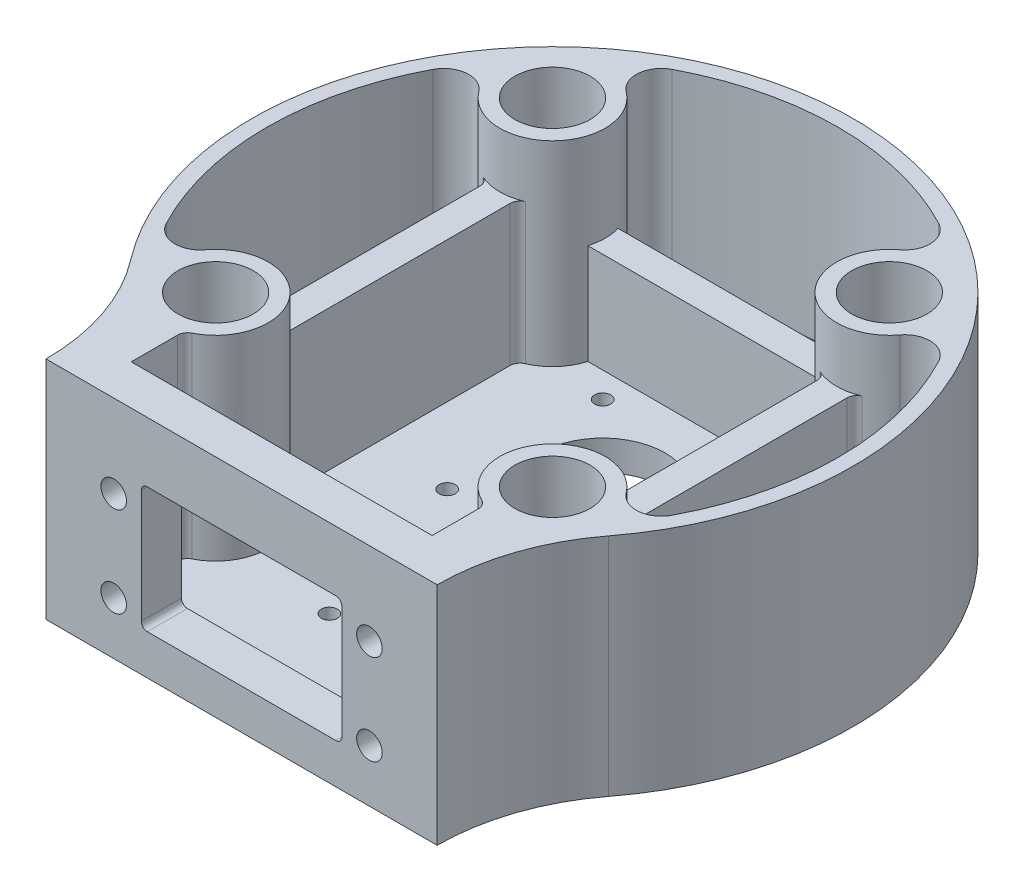
SolidWorks part; units mm, degrees
ref_plane "Front Plane" through (0, 0, 0) normal (0, 0, 1) x (1, 0, 0)
ref_plane "Top Plane" through (0, 0, 0) normal (0, 1, 0) x (1, 0, 0)
ref_plane "Right Plane" through (0, 0, 0) normal (1, 0, 0) x (0, 0, -1)
sketch "Sketch1" plane through (0, 0, 0) normal (0, 1, 0) x (1, 0, 0)
  line L0 (0, 0) -> (0, -60) construction
  line L1 (0, 0) -> (-33.5876, -33.5876) construction
  line L2 (-39, -62) -> (39, -62)
  line L3 (-30, -54) -> (30, -54)
  line L4 (-30, -43.4557) -> (-30, -54)
  line L5 (30, -54) -> (30, -43.4557)
  line L6 (-39, -54) -> (39, -54) construction
  arc A0 (47.6471, -36.4658) -> (-47.6471, -36.4658) centre (0, 0) ccw
  circle A1 centre (-33.5876, -33.5876) radius 7.5
  arc A2 (-36.6953, -43.6171) -> (-43.6171, -36.6953) centre (-33.5876, -33.5876) ccw
  arc A3 (-36.6953, -43.6171) -> (-30, -48.4665) centre (0, 0) ccw
  circle A4 centre (-33.5876, -33.5876) radius 10.5 construction
  circle A5 centre (0, 0) radius 57 construction
  arc A6 (-43.6171, 36.6953) -> (-36.6953, 43.6171) centre (-33.5876, 33.5876) ccw
  circle A7 centre (-33.5876, 33.5876) radius 7.5
  arc A8 (36.6953, 43.6171) -> (43.6171, 36.6953) centre (33.5876, 33.5876) ccw
  circle A9 centre (33.5876, 33.5876) radius 7.5
  arc A10 (43.6171, -36.6953) -> (36.6953, -43.6171) centre (33.5876, -33.5876) ccw
  circle A11 centre (33.5876, -33.5876) radius 7.5
  arc A12 (-43.6171, 36.6953) -> (-43.6171, -36.6953) centre (0, 0) ccw
  arc A13 (36.6953, 43.6171) -> (-36.6953, 43.6171) centre (0, 0) ccw
  arc A14 (43.6171, -36.6953) -> (43.6171, 36.6953) centre (0, 0) ccw
  arc A15 (-39, -62) -> (-47.6471, -36.4658) centre (-81, -61.9919) ccw
  arc A16 (39, -62) -> (47.6471, -36.4658) centre (81, -61.9919) cw
  circle A17 centre (0, 0) radius 60 construction
  arc A19 (30, -48.4665) -> (36.6953, -43.6171) centre (0, 0) ccw
  dimension "D1" = 120
  dimension "D4" = 15
  dimension "D11" = 42
  dimension "D12" = 42
  dimension "D2" = 45
  dimension "D3" = 47.5
  dimension "D8" = 62
  dimension "D9" = 78
  dimension "D10" = 39
  dimension "D14" = 60
  dimension "D15" = 30
  dimension "D5" = 3
  dimension "D6" = 3
  dimension "D13" = 8
  dimension "D7" = 4
extrude "Boss-Extrude1" add sketch "Sketch1" along normal blind 45 contours L2 A16 A0 A15 A19 L5 L3 L4 A3 A2 A12 A6 A13 A8 A14 A10 A1 A7 A9 A11 | L5 A19 A10 | A2 A3 L4
sketch "Sketch2" plane through (0, 0, 0) normal (0, -1, 0) x (1, 0, 0)
  line L1 (39, 62) -> (-39, 62)
  line L2 (39, 62) -> (-39, 62)
  arc A3 (-47.6471, 36.4658) -> (-39, 62) centre (-81, 61.9919) ccw
  arc A4 (-47.6471, 36.4658) -> (47.6471, 36.4658) centre (0, 0) ccw
  arc A5 (39, 62) -> (47.6471, 36.4658) centre (81, 61.9919) ccw
  arc A6 (-47.6471, 36.4658) -> (-39, 62) centre (-81, 61.9919) ccw
  arc A7 (-47.6471, 36.4658) -> (47.6471, 36.4658) centre (0, 0) ccw
  arc A8 (39, 62) -> (47.6471, 36.4658) centre (81, 61.9919) ccw
  dimension "D1" = 0
extrude "Boss-Extrude2" add sketch "Sketch2" against normal blind 6
sketch "Sketch3" plane through (0, 6, 0) normal (0, 1, 0) x (1, 0, 0)
  line L1 (-5.75, -38.75) -> (5.75, -38.75) construction
  line L2 (-5.75, -38.75) -> (-5.75, -27.25) construction
  line L3 (-5.75, -27.25) -> (5.75, -27.25) construction
  line L4 (5.75, -38.75) -> (5.75, -27.25) construction
  line L5 (-5.75, -38.75) -> (5.75, -27.25) construction
  line L6 (-5.75, -27.25) -> (5.75, -38.75) construction
  circle A0 centre (-33.5876, 33.5876) radius 5.25
  circle A1 centre (33.5876, 33.5876) radius 5.25
  circle A2 centre (33.5876, -33.5876) radius 5.25
  circle A3 centre (-33.5876, -33.5876) radius 5.25
  circle A4 centre (0, -33) radius 4.25
  circle A5 centre (-5.75, -27.25) radius 1.6
  circle A6 centre (5.75, -27.25) radius 1.6
  circle A7 centre (5.75, -38.75) radius 1.6
  circle A8 centre (-5.75, -38.75) radius 1.6
  dimension "D1" = 10.5
  dimension "D2" = 10.5
  dimension "D3" = 10.5
  dimension "D4" = 10.5
  dimension "D6" = 8.5
  dimension "D9" = 3.2
  dimension "D10" = 3.2
  dimension "D11" = 3.2
  dimension "D12" = 3.2
  dimension "D5" = 33
  dimension "D7" = 11.5
  dimension "D8" = 11.5
extrude "Cut-Extrude1" cut sketch "Sketch3" against normal through all
fillet "Fillet1" radius 5 6 edges at (-43.6171, 25.5, 36.6953) (43.6171, 25.5, 36.6953) (43.6171, 25.5, -36.6953) (36.6953, 25.5, -43.6171) (-36.6953, 25.5, -43.6171) (-43.6171, 25.5, -36.6953)
sketch "Sketch4" plane through (0, 6, 0) normal (0, 1, 0) x (1, 0, 0)
  circle A0 centre (0, -33) radius 5.1
  dimension "D1" = 10.2
extrude "Cut-Extrude2" cut sketch "Sketch4" against normal blind 2
sketch "Sketch5" plane through (0, 0, 0) normal (0, -1, 0) x (1, 0, 0)
  line L1 (-15.5, 5.5) -> (15.5, 5.5) construction
  line L2 (-15.5, 5.5) -> (-15.5, -25.5) construction
  line L3 (-15.5, -25.5) -> (15.5, -25.5) construction
  line L4 (15.5, 5.5) -> (15.5, -25.5) construction
  line L5 (-15.5, 5.5) -> (15.5, -25.5) construction
  line L6 (-15.5, -25.5) -> (15.5, 5.5) construction
  circle A0 centre (0, -10) radius 12.5
  circle A1 centre (15.5, 5.5) radius 1.6
  circle A2 centre (-15.5, 5.5) radius 1.6
  circle A3 centre (-15.5, -25.5) radius 1.6
  circle A4 centre (15.5, -25.5) radius 1.6
  dimension "D2" = 25
  dimension "D5" = 3.2
  dimension "D6" = 3.2
  dimension "D7" = 3.2
  dimension "D8" = 3.2
  dimension "D1" = 10
  dimension "D3" = 31
  dimension "D4" = 31
extrude "Cut-Extrude3" cut sketch "Sketch5" against normal through all
sketch "Sketch6" plane through (0, 0, 62) normal (0, 0, 1) x (1, 0, 0)
  line L0 (-39, 0) -> (39, 0) construction
  line L1 (-20, 8) -> (20, 8)
  line L2 (-20, 8) -> (-20, 33)
  line L3 (-20, 33) -> (20, 33)
  line L4 (20, 8) -> (20, 33)
  line L5 (-20, 8) -> (20, 33) construction
  line L6 (-20, 33) -> (20, 8) construction
  point P0 (0, 20.5)
  dimension "D1" = 40
  dimension "D2" = 25
  dimension "D3" = 8
extrude "Cut-Extrude4" cut sketch "Sketch6" against normal up to next
sketch "Sketch7" plane through (0, 0, 62) normal (0, 0, 1) x (1, 0, 0)
  line L1 (-20, 33) -> (-20, 8) construction
  line L2 (20, 8) -> (20, 33) construction
  line L4 (-39, 45) -> (39, 45) construction
  circle A0 centre (-25.5, 10.5) radius 2.55
  circle A1 centre (25.5, 10.5) radius 2.55
  circle A2 centre (25.5, 28.5) radius 2.55
  circle A3 centre (-25.5, 28.5) radius 2.55
  dimension "D2" = 5.5
  dimension "D7" = 5.1
  dimension "D8" = 5.1
  dimension "D9" = 5.1
  dimension "D10" = 5.1
  dimension "D3" = 5.5
  dimension "D4" = 5.5
  dimension "D5" = 5.5
  dimension "D6" = 18
  dimension "D11" = 16.5
extrude "Cut-Extrude5" cut sketch "Sketch7" against normal up to next
sketch "Sketch8" plane through (0, 6, 0) normal (0, 1, 0) x (1, 0, 0)
  line L0 (-33.5876, 33.5876) -> (-33.5876, -33.5876) construction
  line L1 (-36.5876, 23.5253) -> (-36.5876, -23.5253)
  line L2 (-30.5876, 23.5253) -> (-30.5876, -23.5253)
  line L3 (33.5876, 33.5876) -> (33.5876, -33.5876) construction
  line L4 (30.5876, 23.5253) -> (30.5876, -23.5253)
  line L5 (36.5876, 23.5253) -> (36.5876, -23.5253)
  line L6 (-36.5876, 33.5876) -> (-36.5876, -33.5876) construction
  line L7 (-30.5876, 33.5876) -> (-30.5876, -33.5876) construction
  line L8 (30.5876, 33.5876) -> (30.5876, -33.5876) construction
  line L9 (36.5876, 33.5876) -> (36.5876, -33.5876) construction
  arc A0 (-30, -43.4557) -> (-41.9844, -27.2833) centre (-33.5876, -33.5876) ccw construction
  arc A1 (41.9844, -27.2833) -> (30, -43.4557) centre (33.5876, -33.5876) ccw construction
  arc A2 (27.2833, 41.9844) -> (41.9844, 27.2833) centre (33.5876, 33.5876) ccw construction
  arc A3 (-41.9844, 27.2833) -> (-27.2833, 41.9844) centre (-33.5876, 33.5876) ccw construction
  arc A4 (-30.5876, -23.5253) -> (-36.5876, -23.5253) centre (-33.5876, -33.5876) ccw
  arc A5 (36.5876, -23.5253) -> (30.5876, -23.5253) centre (33.5876, -33.5876) ccw
  arc A6 (30.5876, 23.5253) -> (36.5876, 23.5253) centre (33.5876, 33.5876) ccw
  arc A7 (-36.5876, 23.5253) -> (-30.5876, 23.5253) centre (-33.5876, 33.5876) ccw
  dimension "D1" = 3
  dimension "D2" = 3
  dimension "D3" = 3
  dimension "D4" = 3
extrude "Boss-Extrude3" add sketch "Sketch8" along normal blind 28
fillet "Fillet2" radius 2 10 edges at (36.5876, 20, 23.5253) (30.5876, 20, 23.5253) (-36.5876, 20, 23.5253) (-30.5876, 20, 23.5253) (30.5876, 20, -23.5253) (36.5876, 20, -23.5253) (-36.5876, 20, -23.5253) (-30.5876, 20, -23.5253) (30, 25.5, 43.4557) (-30, 25.5, 43.4557)
sketch "Sketch9" plane through (0, 6, 0) normal (0, 1, 0) x (1, 0, 0)
  line L0 (-33.5876, 33.5876) -> (33.5876, 33.5876) construction
  line L1 (-23.5253, 30.5876) -> (23.5253, 30.5876)
  line L2 (-23.5253, 36.5876) -> (23.5253, 36.5876)
  line L3 (-33.5876, 36.5876) -> (33.5876, 36.5876) construction
  line L4 (-33.5876, 30.5876) -> (33.5876, 30.5876) construction
  arc A0 (27.2833, 41.9844) -> (41.9844, 27.2833) centre (33.5876, 33.5876) ccw construction
  arc A1 (-29.3876, 23.9642) -> (-27.2833, 41.9844) centre (-33.5876, 33.5876) ccw construction
  arc A2 (23.5253, 36.5876) -> (23.5253, 30.5876) centre (33.5876, 33.5876) ccw
  arc A3 (-23.5253, 30.5876) -> (-23.5253, 36.5876) centre (-33.5876, 33.5876) ccw
  dimension "D1" = 3
  dimension "D2" = 3
extrude "Boss-Extrude4" add sketch "Sketch9" along normal blind 20
fillet "Fillet3" radius 1.2 4 edges at (20, 8, 58) (20, 33, 58) (-20, 8, 58) (-20, 33, 58)
